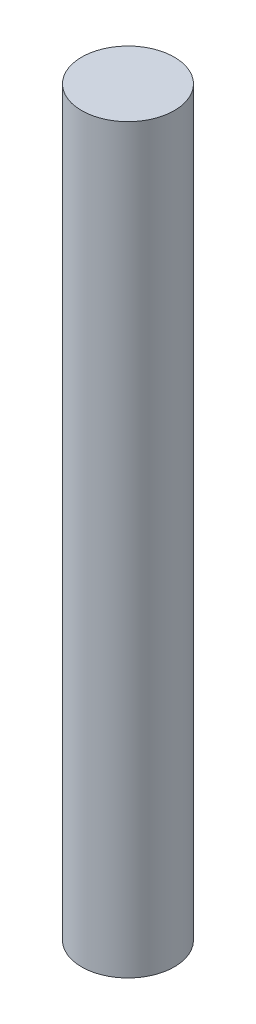
SolidWorks part; units mm, degrees
ref_plane "Front Plane" through (0, 0, 0) normal (0, 0, 1) x (1, 0, 0)
ref_plane "Top Plane" through (0, 0, 0) normal (0, 1, 0) x (1, 0, 0)
ref_plane "Right Plane" through (0, 0, 0) normal (1, 0, 0) x (0, 0, -1)
sketch "Sketch1" plane through (0, 0, 0) normal (0, 1, 0) x (1, 0, 0)
  circle A0 centre (0, 0) radius 4.7625
  dimension "D1" = 9.525
extrude "Boss-Extrude1" add sketch "Sketch1" along normal blind 76.2
